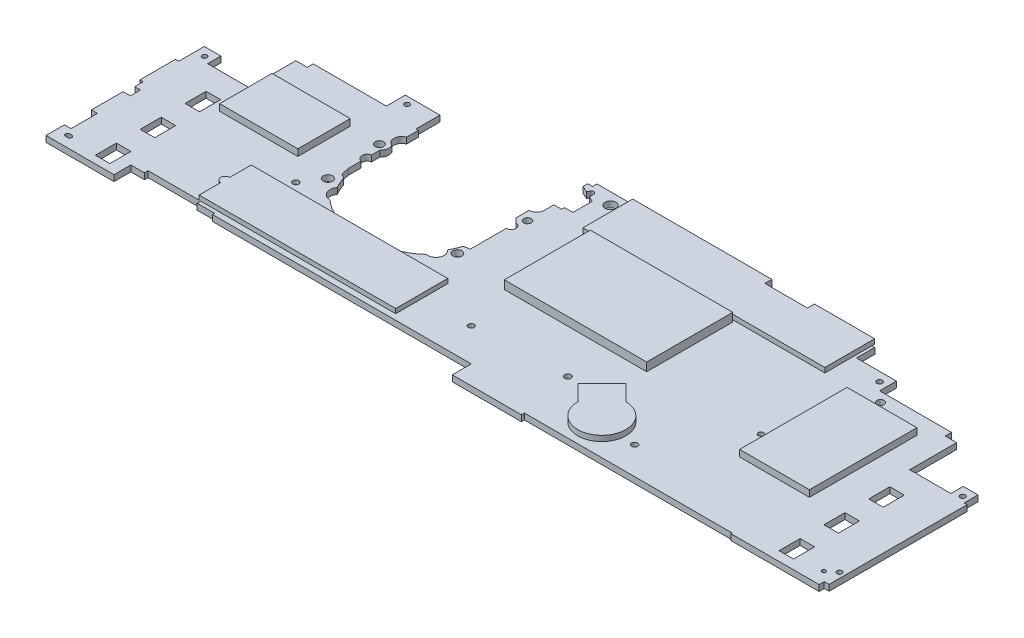
SolidWorks part; units mm, degrees
ref_plane "Front Plane" through (0, 0, 0) normal (0, 0, 1) x (1, 0, 0)
ref_plane "Top Plane" through (0, 0, 0) normal (0, 1, 0) x (1, 0, 0)
ref_plane "Right Plane" through (0, 0, 0) normal (1, 0, 0) x (0, 0, -1)
sketch "Sketch1" plane through (0, 0, 0) normal (0, 1, 0) x (1, 0, 0)
  line L0 (0, 0) -> (0, 100.33) construction
  line L1 (0, 0) -> (29.21, 0)
  line L2 (29.21, 1.27) -> (116.84, 1.27)
  line L3 (29.21, 1.27) -> (29.21, 0)
  line L4 (0, 0) -> (0, 8.001)
  line L5 (0, 8.001) -> (-109.22, 8.001)
  line L6 (-109.22, 8.001) -> (-109.22, 8.89)
  line L7 (-109.22, 8.89) -> (-116.586, 8.89)
  line L8 (-116.586, 8.89) -> (-116.586, 10.414)
  line L9 (-116.586, 10.414) -> (-138.811, 10.414)
  line L10 (-138.811, 10.414) -> (-138.811, 8.89)
  line L11 (-138.811, 8.89) -> (-144.526, 8.89)
  line L12 (-144.526, 8.89) -> (-144.526, 1.778)
  line L13 (-144.526, 1.778) -> (-173.228, 1.778)
  line L14 (116.84, 1.27) -> (116.84, 0.762)
  line L15 (116.84, 0.762) -> (154.051, 0.762)
  line L16 (-39.243, 100.33) -> (34.544, 100.33)
  line L17 (34.544, 100.33) -> (34.544, 99.187)
  line L18 (34.544, 99.187) -> (35.687, 99.187)
  line L19 (35.687, 99.187) -> (35.687, 98.044)
  line L20 (35.687, 98.044) -> (42.799, 98.044)
  line L21 (42.799, 98.044) -> (42.799, 99.187)
  line L22 (42.799, 99.187) -> (79.121, 99.187)
  line L23 (79.121, 99.187) -> (79.121, 91.44)
  line L24 (79.121, 91.44) -> (96.012, 91.44)
  line L25 (96.012, 91.44) -> (96.012, 84.328)
  line L26 (96.012, 84.328) -> (126.365, 84.328)
  line L27 (126.365, 84.328) -> (126.365, 81.661)
  line L28 (126.365, 81.661) -> (131.191, 81.661)
  line L29 (131.191, 81.661) -> (131.191, 61.849)
  line L30 (131.191, 61.849) -> (148.59, 61.849)
  line L31 (148.59, 61.849) -> (148.59, 67.056)
  line L32 (148.59, 67.056) -> (154.813, 67.056)
  line L33 (154.813, 67.056) -> (154.813, 61.214)
  line L34 (154.813, 61.214) -> (156.083, 61.214)
  line L35 (154.051, 0.762) -> (154.051, 2.921)
  line L36 (154.051, 2.921) -> (156.083, 2.921)
  line L37 (156.083, 2.921) -> (156.083, 61.214)
  line L38 (-39.243, 100.33) -> (-39.2553, 98.432)
  line L39 (-39.2553, 98.432) -> (-41.2873, 98.432)
  line L40 (-41.2873, 98.432) -> (-41.2873, 96.527)
  line L41 (-41.2873, 96.527) -> (-38.6563, 95.2457)
  line L42 (-38.6563, 95.2457) -> (-36.201, 94.05) construction
  line L43 (-36.201, 94.05) -> (-33.909, 92.9338)
  line L44 (-33.909, 92.9338) -> (-33.909, 84.8378)
  line L45 (-33.909, 84.8378) -> (-37.4281, 84.8378)
  line L46 (-37.4281, 84.8378) -> (-37.4281, 83.5928)
  line L47 (-37.4281, 83.5928) -> (-40.7148, 83.5928)
  line L48 (-40.7148, 83.5928) -> (-40.7148, 79.5373)
  line L49 (-97.536, 82.169) -> (-97.536, 92.329)
  line L50 (-97.536, 92.329) -> (-112.141, 92.329)
  line L51 (-112.141, 92.329) -> (-112.141, 84.328)
  line L52 (-112.141, 84.328) -> (-143.002, 84.328)
  line L53 (-143.002, 84.328) -> (-143.002, 81.788)
  line L54 (-143.002, 81.788) -> (-147.828, 81.788)
  line L55 (-147.828, 81.788) -> (-147.828, 62.103)
  line L56 (-81.8406, 33.401) -> (-58.4726, 33.401)
  line L57 (-147.828, 62.103) -> (-165.354, 62.103)
  line L58 (-165.354, 62.103) -> (-165.354, 67.691)
  line L59 (-165.354, 67.691) -> (-172.339, 67.691)
  line L60 (-172.339, 67.691) -> (-172.339, 56.896)
  line L61 (-172.339, 56.896) -> (-173.736, 56.896)
  line L62 (-173.736, 56.896) -> (-173.736, 41.91)
  line L63 (-173.736, 41.91) -> (-172.339, 41.91)
  line L64 (-172.339, 41.91) -> (-172.339, 38.354)
  line L65 (-172.339, 38.354) -> (-169.926, 38.354)
  line L66 (-169.926, 38.354) -> (-169.926, 34.036)
  line L67 (-169.926, 34.036) -> (-172.974, 34.036)
  line L68 (-172.974, 34.036) -> (-172.974, 20.701)
  line L69 (-172.974, 20.701) -> (-170.434, 20.701)
  line L70 (-170.434, 20.701) -> (-170.434, 9.525)
  line L71 (-170.434, 9.525) -> (-173.228, 9.525)
  line L72 (-173.228, 9.525) -> (-173.228, 1.778)
  line L73 (619.4004, -63.6761) -> (919.3489, -63.6761) construction
  line L74 (386.1344, 2016.6403) -> (2402.1344, 2016.6403) construction
  line L75 (-97.536, 82.169) -> (-96.52, 82.169)
  line L76 (-96.52, 82.169) -> (-96.52, 77.2147)
  line L77 (-43.9251, 76.327) -> (-43.9251, 70.7822)
  line L78 (-43.9251, 70.7822) -> (-42.1421, 69.0339)
  line L79 (-42.1421, 64.897) -> (-42.1421, 49.657)
  line L80 (-42.1421, 49.657) -> (-44.6572, 49.3821)
  line L81 (-97.385, 66.8989) -> (-97.385, 63.3433)
  line L82 (-96.52, 49.9446) -> (-94.8905, 49.0804)
  line L83 (-36.1922, 95.9135) -> (-36.0671, 94.5448)
  line L84 (-38.0463, 96.3803) -> (-38.6563, 95.2457)
  line L85 (-97.385, 58.928) -> (-97.385, 53.3696)
  line L86 (-97.385, 53.3696) -> (-96.52, 49.9446)
  line L87 (134.7258, 1008.6621) -> (1142.7258, 1008.6621) construction
  circle A0 centre (-37.4286, 94.6478) radius 1.3654
  arc A1 (-40.7148, 79.5373) -> (-43.9251, 76.327) centre (-43.9251, 79.5373) cw
  arc A3 (-42.1421, 69.0339) -> (-42.1421, 64.897) centre (-42.1421, 66.9655) cw
  arc A4 (-58.4726, 33.401) -> (-49.4828, 38.5603) centre (-65.2102, 55.553) ccw
  arc A5 (-44.6572, 49.3821) -> (-46.7116, 44.6759) centre (-65.2102, 55.553) cw
  arc A6 (-46.7116, 44.6759) -> (-49.4828, 38.5603) centre (-48.8036, 41.9382) cw
  arc A7 (-96.52, 77.2147) -> (-96.65, 71.12) centre (-95.5186, 74.1446) ccw
  arc A8 (-96.65, 71.12) -> (-97.385, 66.8989) centre (-99.5486, 69.4502) cw
  arc A9 (-97.385, 63.3433) -> (-97.385, 58.928) centre (-96.9951, 61.1357) ccw
  circle A10 centre (-37.178, 95.9135) radius 0.9858
  arc A11 (-94.8905, 49.0804) -> (-92.7312, 44.222) centre (-74.192, 55.3707) ccw
  arc A12 (-81.8406, 33.401) -> (-89.7037, 38.1) centre (-74.0723, 55.3286) cw
  arc A13 (-89.7037, 38.1) -> (-92.7312, 44.222) centre (-89.7029, 41.91) cw
  point P64 (-37.178, 96.8993)
  point P98 (-38.1638, 95.9135)
  point P103 (-36.1922, 95.9135)
  point P156 (-96.65, 71.12)
  dimension "D38" = 68.326
  dimension "D52" = 84.328
  dimension "D56" = 14.605
  dimension "D60" = 2.54
  dimension "D77" = 30.099
  dimension "D91" = 23.368
  dimension "D80" = 63.119
  dimension "D2" = 29.21
  dimension "D3" = 87.63
  dimension "D4" = 1.27
  dimension "D5" = 8.001
  dimension "D6" = 109.22
  dimension "D7" = 0.889
  dimension "D8" = 1.524
  dimension "D9" = 7.112
  dimension "D10" = 1.524
  dimension "D11" = 7.366
  dimension "D12" = 22.225
  dimension "D13" = 5.715
  dimension "D14" = 28.702
  dimension "D15" = 37.211
  dimension "D16" = 0.508
  dimension "D17" = 73.787
  dimension "D18" = 1.143
  dimension "D19" = 1.143
  dimension "D20" = 1.143
  dimension "D21" = 1.143
  dimension "D22" = 7.112
  dimension "D23" = 36.322
  dimension "D24" = 7.747
  dimension "D25" = 16.891
  dimension "D26" = 7.112
  dimension "D27" = 35.179
  dimension "D28" = 4.826
  dimension "D29" = 2.667
  dimension "D30" = 19.812
  dimension "D31" = 17.399
  dimension "D32" = 5.207
  dimension "D33" = 6.223
  dimension "D34" = 5.842
  dimension "D35" = 1.27
  dimension "D36" = 2.032
  dimension "D37" = 58.293
  dimension "D39" = 2.032
  dimension "D49" = 63.627
  dimension "D53" = 10.16
  dimension "D54" = 8.001
  dimension "D55" = 100.33
  dimension "D57" = 35.687
  dimension "D58" = 4.826
  dimension "D59" = 25.4
  dimension "D61" = 19.685
  dimension "D62" = 1.016
  dimension "D63" = 17.526
  dimension "D64" = 5.588
  dimension "D65" = 6.985
  dimension "D66" = 10.795
  dimension "D67" = 1.397
  dimension "D68" = 14.986
  dimension "D69" = 3.556
  dimension "D70" = 1.397
  dimension "D71" = 3.81
  dimension "D72" = 0.762
  dimension "D73" = 7.874
  dimension "D74" = 13.335
  dimension "D75" = 2.794
  dimension "D76" = 11.176
  dimension "D78" = 41.656
  dimension "D79" = 50.927
extrude "Boss-Extrude1" add sketch "Sketch1" along normal blind 2.54
ref_plane "Plane1" through (0, 1.27, 0) normal (0, 1, 0) x (1, 0, 0)
sketch "Sketch3" plane through (0, 1.27, 0) normal (0, 1, 0) x (1, 0, 0)
  line L0 (14.605, 0) -> (14.605, 100.33) construction
  line L1 (0, 0) -> (29.21, 0) construction
  line L2 (-39.243, 100.33) -> (34.544, 100.33) construction
  line L3 (192.405, 50.165) -> (-213.995, 50.165)
  line L4 (-170.434, 20.701) -> (-170.434, 9.525) construction
  line L5 (-155.575, 51.689) -> (-149.479, 51.689)
  line L6 (-155.575, 51.689) -> (-155.575, 42.799)
  line L7 (-155.575, 42.799) -> (-149.479, 42.799)
  line L8 (-149.479, 51.689) -> (-149.479, 42.799)
  line L9 (-155.575, 32.766) -> (-149.479, 32.766)
  line L10 (-155.575, 32.766) -> (-155.575, 23.876)
  line L11 (-155.575, 23.876) -> (-149.479, 23.876)
  line L12 (-149.479, 32.766) -> (-149.479, 23.876)
  line L13 (-155.575, 13.843) -> (-149.479, 13.843)
  line L14 (-155.575, 13.843) -> (-155.575, 4.953)
  line L15 (-155.575, 4.953) -> (-149.479, 4.953)
  line L16 (-149.479, 13.843) -> (-149.479, 4.953)
  line L17 (133.223, 51.435) -> (139.319, 51.435)
  line L18 (133.223, 51.435) -> (133.223, 42.545)
  line L19 (133.223, 42.545) -> (139.319, 42.545)
  line L20 (139.319, 51.435) -> (139.319, 42.545)
  line L21 (133.223, 32.512) -> (139.319, 32.512)
  line L22 (133.223, 32.512) -> (133.223, 23.622)
  line L23 (133.223, 23.622) -> (139.319, 23.622)
  line L24 (139.319, 32.512) -> (139.319, 23.622)
  line L25 (133.223, 13.589) -> (139.319, 13.589)
  line L26 (133.223, 13.589) -> (133.223, 4.699)
  line L27 (133.223, 4.699) -> (139.319, 4.699)
  line L28 (139.319, 13.589) -> (139.319, 4.699)
  line L29 (156.083, 2.921) -> (156.083, 61.214) construction
  line L30 (131.191, 61.849) -> (148.59, 61.849) construction
  line L31 (-147.828, 62.103) -> (-165.354, 62.103) construction
  line L32 (154.813, 67.056) -> (154.813, 61.214) construction
  line L37 (148.59, 61.849) -> (148.59, 67.056) construction
  line L38 (148.59, 67.056) -> (154.813, 67.056) construction
  line L39 (131.191, 81.661) -> (131.191, 61.849) construction
  line L40 (96.012, 84.328) -> (126.365, 84.328) construction
  line L41 (29.21, 1.27) -> (116.84, 1.27) construction
  line L42 (96.012, 91.44) -> (96.012, 84.328) construction
  line L43 (79.121, 91.44) -> (96.012, 91.44) construction
  line L44 (42.799, 99.187) -> (79.121, 99.187) construction
  line L45 (-41.2873, 98.432) -> (-41.2873, 96.527) construction
  line L46 (0, 8.001) -> (-109.22, 8.001) construction
  line L47 (-147.828, 81.788) -> (-147.828, 62.103) construction
  line L49 (-109.22, 8.89) -> (-116.586, 8.89) construction
  line L50 (-97.536, 92.329) -> (-112.141, 92.329) construction
  line L51 (-112.141, 92.329) -> (-112.141, 84.328) construction
  line L52 (-168.783, 6.477) -> (-167.894, 6.477) construction
  line L54 (-172.339, 41.91) -> (-172.339, 38.354) construction
  line L56 (-172.339, 67.691) -> (-172.339, 56.896) construction
  line L57 (-165.354, 62.103) -> (-165.354, 67.691) construction
  line L58 (-165.354, 67.691) -> (-172.339, 67.691) construction
  line L59 (-173.228, 9.525) -> (-173.228, 1.778) construction
  line L60 (-168.783, 7.366) -> (-167.894, 7.366)
  line L61 (-168.783, 5.588) -> (-167.894, 5.588)
  circle A0 centre (153.8605, 9.5885) radius 1.0795
  circle A1 centre (150.1775, 6.6675) radius 0.8255
  circle A2 centre (152.0825, 63.3095) radius 1.0795
  circle A3 centre (92.71, 87.63) radius 1.143
  circle A4 centre (100.457, 80.264) radius 1.524
  circle A5 centre (86.8045, 43.4975) radius 0.9525
  circle A6 centre (64.008, 12.954) radius 1.27
  circle A7 centre (24.9555, 23.8125) radius 1.3335
  circle A8 centre (-13.9065, 21.9075) radius 1.2065
  circle A9 centre (-43.307, 45.466) radius 1.905
  circle A10 centre (-40.4495, 72.1995) radius 1.5875
  circle A11 centre (-28.5873, 95.377) radius 2.286
  circle A12 centre (-108.3945, 89.3445) radius 1.0795
  circle A13 centre (-99.695, 68.961) radius 1.778
  circle A14 centre (-97.9805, 45.5295) radius 1.9685
  circle A15 centre (-103.378, 37.338) radius 1.27
  circle A17 centre (-168.656, 64.135) radius 1.016
  circle A18 centre (86.8045, 43.4975) radius 1.143
  arc A21 (-168.783, 7.366) -> (-168.783, 5.588) centre (-168.783, 6.477) ccw
  arc A22 (-167.894, 5.588) -> (-167.894, 7.366) centre (-167.894, 6.477) ccw
  point P8 (14.605, 50.165)
  point P9 (14.605, 50.165)
  point P74 (-165.4142, 7.366)
  point P75 (-165.4142, 5.588)
  point P78 (152.0825, 64.389)
  point P79 (151.003, 63.3095)
  point P80 (152.0825, 62.23)
  point P81 (153.162, 63.3095)
  point P88 (153.8605, 10.668)
  point P89 (154.94, 9.5885)
  point P90 (153.8605, 8.509)
  point P91 (152.781, 9.5885)
  point P92 (151.003, 6.6675)
  point P93 (150.1775, 7.493)
  point P94 (150.1775, 5.842)
  point P95 (149.352, 6.6675)
  point P96 (100.457, 81.788)
  point P97 (98.933, 80.264)
  point P98 (100.457, 78.74)
  point P99 (101.981, 80.264)
  point P100 (92.71, 88.773)
  point P101 (93.853, 87.63)
  point P102 (92.71, 86.487)
  point P103 (91.567, 87.63)
  point P104 (86.8045, 44.45)
  point P105 (87.757, 43.4975)
  point P106 (86.8045, 42.545)
  point P107 (85.852, 43.4975)
  point P119 (64.008, 14.224)
  point P122 (65.278, 12.954)
  point P123 (62.738, 12.954)
  point P124 (64.008, 11.684)
  point P125 (24.9555, 22.479)
  point P126 (26.289, 23.8125)
  point P127 (23.622, 23.8125)
  point P128 (24.9555, 25.146)
  point P129 (-13.9065, 23.114)
  point P130 (-15.113, 21.9075)
  point P131 (-13.9065, 20.701)
  point P132 (-12.7, 21.9075)
  point P133 (-43.307, 43.561)
  point P134 (-41.402, 45.466)
  point P135 (-45.212, 45.466)
  point P136 (-43.307, 47.371)
  point P137 (-42.037, 72.1995)
  point P138 (-40.4495, 70.612)
  point P139 (-38.862, 72.1995)
  point P140 (-40.4495, 73.787)
  point P141 (-30.8733, 95.377)
  point P142 (-28.5873, 97.663)
  point P143 (-26.3013, 95.377)
  point P144 (-28.5873, 93.091)
  point P145 (-109.474, 89.3445)
  point P146 (-108.3945, 90.424)
  point P147 (-107.315, 89.3445)
  point P148 (-108.3945, 88.265)
  point P149 (-99.695, 70.739)
  point P150 (-101.473, 68.961)
  point P151 (-99.695, 67.183)
  point P152 (-97.917, 68.961)
  point P153 (-97.9805, 47.498)
  point P154 (-99.949, 45.5295)
  point P155 (-97.9805, 43.561)
  point P156 (-96.012, 45.5295)
  point P157 (-103.378, 38.608)
  point P158 (-102.108, 37.338)
  point P159 (-103.378, 36.068)
  point P160 (-104.648, 37.338)
  point P163 (-168.3385, 6.477)
  point P165 (-168.656, 65.151)
  point P166 (-169.672, 64.135)
  point P167 (-168.656, 63.119)
  point P168 (-167.64, 64.135)
  point P193 (-169.672, 6.477)
  point P203 (-167.005, 6.477)
  dimension "D23" = 1.651
  dimension "D40" = 2.286
  dimension "D65" = 53.721
  dimension "D1" = 228.6
  dimension "D2" = 177.8
  dimension "D3" = 8.89
  dimension "D4" = 8.89
  dimension "D5" = 8.89
  dimension "D6" = 8.89
  dimension "D7" = 8.89
  dimension "D8" = 8.89
  dimension "D9" = 6.096
  dimension "D10" = 6.096
  dimension "D11" = 6.096
  dimension "D12" = 6.096
  dimension "D13" = 6.096
  dimension "D14" = 6.096
  dimension "D15" = 14.859
  dimension "D16" = 16.764
  dimension "D17" = 10.414
  dimension "D18" = 10.033
  dimension "D19" = 10.033
  dimension "D20" = 10.414
  dimension "D21" = 10.033
  dimension "D22" = 10.033
  dimension "D24" = 2.413
  dimension "D25" = 2.667
  dimension "D26" = 1.143
  dimension "D27" = 56.388
  dimension "D28" = 13.462
  dimension "D29" = 10.033
  dimension "D30" = 5.08
  dimension "D31" = 59.563
  dimension "D32" = 29.21
  dimension "D33" = 2.54
  dimension "D34" = 77.47
  dimension "D35" = 85.217
  dimension "D36" = 2.159
  dimension "D37" = 2.667
  dimension "D38" = 46.99
  dimension "D39" = 41.275
  dimension "D41" = 68.326
  dimension "D42" = 84.963
  dimension "D43" = 67.945
  dimension "D44" = 10.414
  dimension "D45" = 129.794
  dimension "D46" = 22.479
  dimension "D47" = 75.184
  dimension "D48" = 2.667
  dimension "D49" = 10.414
  dimension "D50" = 85.09
  dimension "D51" = 26.543
  dimension "D52" = 62.611
  dimension "D53" = 105.791
  dimension "D54" = 35.56
  dimension "D55" = 104.267
  dimension "D56" = 39.37
  dimension "D57" = 12.7
  dimension "D58" = 77.216
  dimension "D59" = 134.366
  dimension "D60" = 28.067
  dimension "D61" = 35.56
  dimension "D62" = 59.182
  dimension "D63" = 79.375
  dimension "D64" = 44.831
  dimension "D66" = 21.59
  dimension "D67" = 1.905
  dimension "D68" = 2.667
  dimension "D69" = 46.355
  dimension "D70" = 49.53
  dimension "D71" = 67.691
  dimension "D72" = 2.667
  dimension "D73" = 2.286
  dimension "D74" = 2.54
  dimension "D75" = 3.556
  dimension "D76" = 1.778
  dimension "D77" = 60.325
  dimension "D78" = 2.667
extrude "Cut-Extrude1" cut sketch "Sketch3" along normal through all both and the other way through all contours L61 A22 L60 A21 | L16 L13 L14 L15 | L12 L9 L10 L11 | L8 L3 L6 L7 | A17 | A12 | A13 | A14 | A15 | A9 | A11 | A10 | A8 | A7 | A3 | A4 | A6 | A5 | A18 A5 | L28 L25 L26 L27 | L24 L21 L22 L23 | L20 L3 L18 L19 | A2 | A0 | A1 | L20 L17 L18 L3 | L8 L5 L6 L3
sketch "Sketch4" plane through (0, 2.54, 0) normal (0, 1, 0) x (1, 0, 0)
  line L0 (-149.479, 13.843) -> (-149.479, 4.953) construction
  line L1 (-117.221, 32.385) -> (-34.29, 32.385)
  line L2 (-117.221, 32.385) -> (-117.221, 10.414)
  line L3 (-117.221, 10.414) -> (-34.29, 10.414)
  line L4 (-34.29, 32.385) -> (-34.29, 10.414)
  line L5 (0, 8.001) -> (-109.22, 8.001) construction
  circle A0 centre (-117.221, 21.3995) radius 1.905
  dimension "D1" = 3.81
  dimension "D2" = 21.971
  dimension "D3" = 82.931
  dimension "D4" = 115.189
  dimension "D5" = 2.413
extrude "Boss-Extrude2" add sketch "Sketch4" along normal blind 1.905 contours A0 L2 L3 L4 L1 | L2 A0 | L2 A0
sketch "Sketch5" plane through (0, 2.54, 0) normal (0, 1, 0) x (1, 0, 0)
  line L0 (-39.243, 100.33) -> (34.544, 100.33) construction
  line L1 (-24.187, 100.33) -> (77.921, 100.33)
  line L2 (-24.187, 100.33) -> (-24.187, 79.33)
  line L3 (-24.187, 79.33) -> (77.921, 79.33)
  line L4 (77.921, 100.33) -> (77.921, 79.33)
  line L5 (79.121, 99.187) -> (79.121, 91.44) construction
  line L7 (34.544, 100.33) -> (52.5215, 100.33)
  line L8 (34.544, 100.33) -> (34.544, 97.3817)
  line L9 (34.544, 97.3817) -> (52.5215, 97.3817)
  line L10 (52.5215, 100.33) -> (52.5215, 97.3817)
  dimension "D1" = 102.108
  dimension "D2" = 21
  dimension "D3" = 1.2
extrude "Boss-Extrude3" add sketch "Sketch5" along normal blind 2 contours L1 L10 L9 L8 L2 L3 L4
sketch "Sketch6" plane through (0, 2.54, 0) normal (0, 1, 0) x (1, 0, 0)
  line L0 (0, 8.001) -> (-109.22, 8.001) construction
  line L1 (-20.193, 78.486) -> (39.878, 78.486)
  line L2 (-20.193, 78.486) -> (-20.193, 42.164)
  line L3 (-20.193, 42.164) -> (39.878, 42.164)
  line L4 (39.878, 78.486) -> (39.878, 42.164)
  line L5 (131.191, 81.661) -> (131.191, 61.849) construction
  dimension "D1" = 60.071
  dimension "D2" = 36.322
  dimension "D3" = 34.163
  dimension "D4" = 91.313
extrude "Boss-Extrude4" add sketch "Sketch6" along normal blind 3.556
sketch "Sketch7" plane through (0, 2.54, 0) normal (0, 1, 0) x (1, 0, 0)
  line L0 (131.191, 81.661) -> (131.191, 61.849) construction
  line L1 (90.678, 75.946) -> (120.142, 75.946)
  line L2 (90.678, 75.946) -> (90.678, 30.607)
  line L3 (90.678, 30.607) -> (120.142, 30.607)
  line L4 (120.142, 75.946) -> (120.142, 30.607)
  line L5 (96.012, 84.328) -> (126.365, 84.328) construction
  dimension "D1" = 29.464
  dimension "D2" = 45.339
  dimension "D3" = 11.049
  dimension "D4" = 8.382
extrude "Boss-Extrude5" add sketch "Sketch7" along normal blind 2.794
sketch "Sketch8" plane through (0, 2.54, 0) normal (0, 1, 0) x (1, 0, 0)
  line L0 (-112.141, 84.328) -> (-143.002, 84.328) construction
  line L1 (-145.415, 69.342) -> (-112.395, 69.342)
  line L2 (-145.415, 69.342) -> (-145.415, 47.242)
  line L3 (-145.415, 47.242) -> (-112.395, 47.242)
  line L4 (-112.395, 69.342) -> (-112.395, 47.242)
  line L5 (-147.828, 81.788) -> (-147.828, 62.103) construction
  dimension "D1" = 33.02
  dimension "D2" = 22.1
  dimension "D3" = 14.986
  dimension "D4" = 2.413
extrude "Boss-Extrude6" add sketch "Sketch8" along normal blind 2.794
sketch "Sketch9" plane through (0, 2.54, 0) normal (0, 1, 0) x (1, 0, 0)
  line L0 (38.608, 14.351) -> (32.0137, 20.9453)
  line L1 (32.0137, 20.9453) -> (42.1737, 31.1053)
  line L2 (42.1737, 31.1053) -> (48.768, 24.511)
  line L3 (37.0937, 26.0253) -> (55.9522, 7.1668) construction
  line L4 (29.21, 1.27) -> (116.84, 1.27) construction
  line L5 (156.083, 2.921) -> (156.083, 61.214) construction
  circle A0 centre (48.768, 14.351) radius 10.16
  point P4 (55.9522, 7.1668)
  point P9 (48.768, 4.191)
  point P10 (58.928, 14.351)
  dimension "D1" = 20.32
  dimension "D2" = 26.67
  dimension "D3" = 2.921
  dimension "D4" = 97.155
  dimension "D5" = 135
extrude "Boss-Extrude7" add sketch "Sketch9" along normal blind 2.286 contours L1 L3 A0 L2 | A0 L3 | L3 L1 L0 A0 | L3 A0
